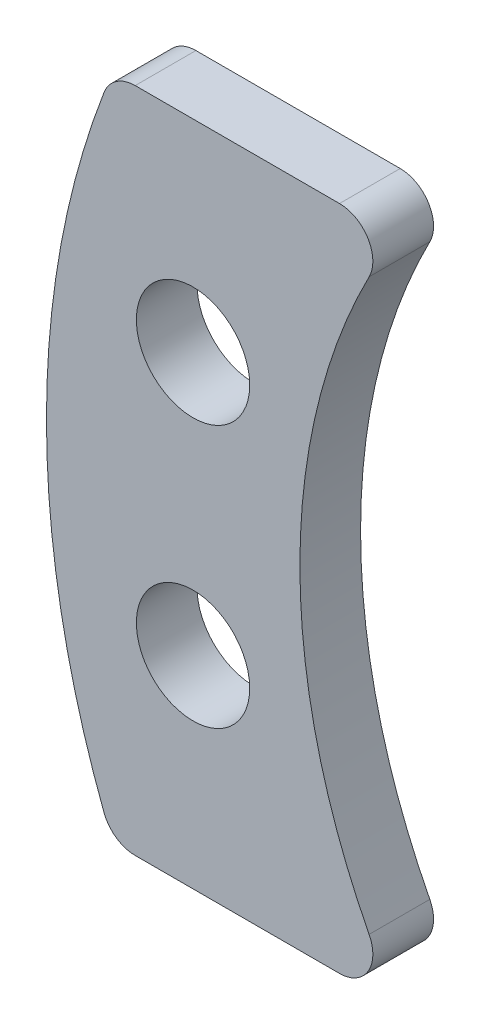
SolidWorks part; units mm, degrees
ref_plane "Front Plane" through (0, 0, 0) normal (0, 0, 1) x (1, 0, 0)
ref_plane "Top Plane" through (0, 0, 0) normal (0, 1, 0) x (1, 0, 0)
ref_plane "Right Plane" through (0, 0, 0) normal (1, 0, 0) x (0, 0, -1)
sketch "Sketch1" plane through (0, 0, 0) normal (0, 0, 1) x (1, 0, 0)
  line L0 (12.0702, 25.4) -> (1.2306, 25.4)
  line L1 (0, 25.4) -> (12.0702, 25.4) construction
  line L2 (0, 25.4) -> (0, 0) construction
  line L3 (0, 0) -> (12.0702, 0) construction
  line L4 (12.0702, 25.4) -> (12.0702, 0) construction
  line L5 (12.0702, 0) -> (1.2306, 0)
  line L7 (0, 12.7) -> (4.295, 12.7) construction
  line L8 (4.295, 17.7) -> (4.295, 7.7) construction
  arc A0 (12.0702, 25.4) -> (12.0702, 0) centre (31.9878, 12.7) ccw
  circle A2 centre (4.295, 17.7) radius 2.159
  circle A3 centre (4.295, 7.7) radius 2.159
  arc A6 (1.2306, 25.4) -> (1.2306, 0) centre (31.9878, 12.7) ccw
  dimension "D3" = 25.4
  dimension "D6" = 4.318
  dimension "D2" = 23.622
  dimension "D1" = 10.8396
  dimension "D4" = 4.295
  dimension "D5" = 10
  dimension "D8" = 12.0702
extrude "Boss-Extrude1" add sketch "Sketch1" along normal blind 2.3114
fillet "Fillet2" radius 1.27 4 edges at (1.2306, 0, 1.1557) (12.0702, 0, 1.1557) (1.2306, 25.4, 1.1557) (12.0702, 25.4, 1.1557)
